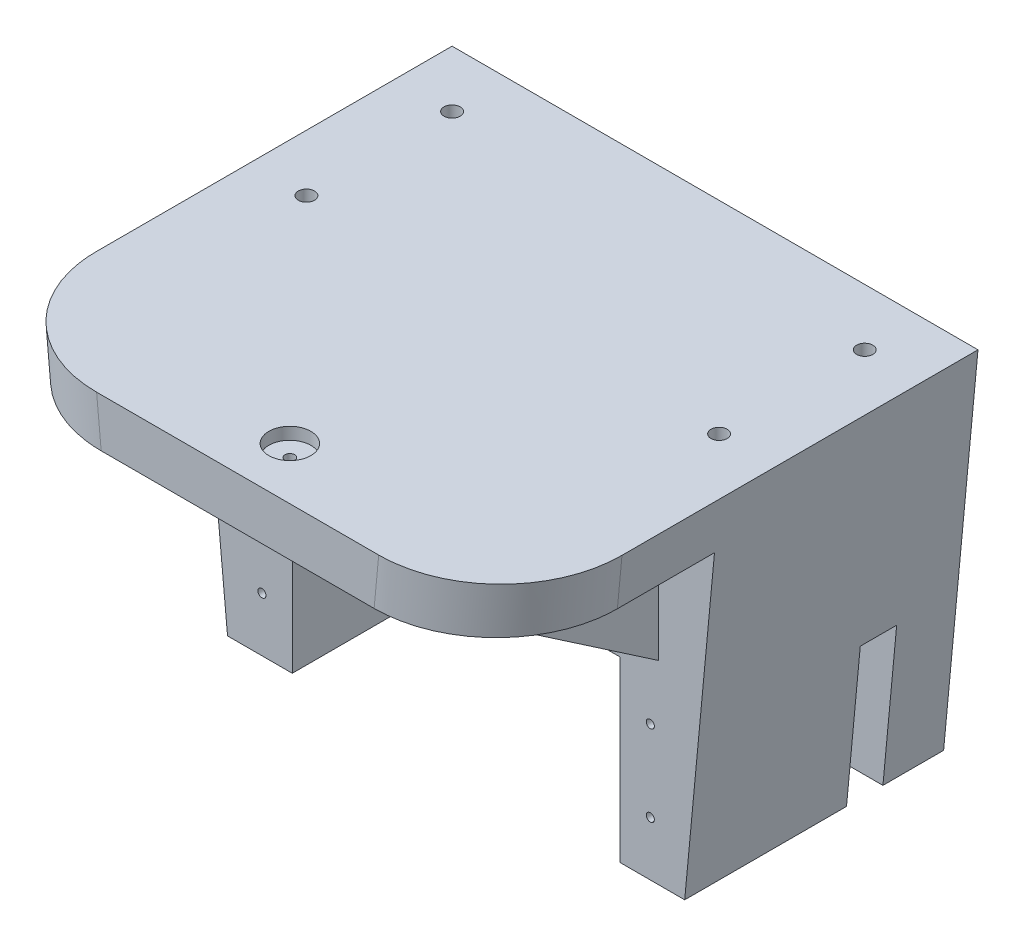
SolidWorks part; units mm, degrees
ref_plane "Plano frontal" through (0, 0, 0) normal (0, 0, 1) x (1, 0, 0)
ref_plane "Plano superior" through (0, 0, 0) normal (0, 1, 0) x (1, 0, 0)
ref_plane "Plano direito" through (0, 0, 0) normal (1, 0, 0) x (0, 0, -1)
sketch "Esboço1" plane through (0, 0, 0) normal (0, 0, 1) x (1, 0, 0)
  line L0 (-32.5, 31.3195) -> (32.5, 31.3195)
  line L1 (32.5, 31.3195) -> (28.25, -13.6805)
  line L2 (28.25, -13.6805) -> (20.25, -13.6805)
  line L3 (20.25, -13.6805) -> (20.25, 8.3195)
  line L4 (20.25, 8.3195) -> (-20.25, 8.3195)
  line L5 (-20.25, 8.3195) -> (-20.25, -13.6805)
  line L6 (-20.25, -13.6805) -> (-28.25, -13.6805)
  line L7 (-28.25, -13.6805) -> (-32.5, 31.3195)
  point P6 (0, 8.3195)
  point P9 (0, 31.3195)
  dimension "D1" = 40.5
  dimension "D2" = 22
  dimension "D3" = 8
  dimension "D4" = 8
  dimension "D5" = 65
  dimension "D6" = 22
  dimension "D7" = 45
extrude "Ressalto-extrusão1" add sketch "Esboço1" along normal blind 30
ref_plane "Plano1" through (40, 0, 0) normal (1, 0, 0) x (0, 0, -1)
sketch "Esboço3" plane through (40, 0, 0) normal (1, 0, 0) x (0, 0, -1)
  line L0 (-10, -13.6805) -> (-10, 4.3195)
  line L1 (-30, -13.6805) -> (0, -13.6805) construction
  line L2 (-10, 4.3195) -> (-5.5, 4.3195)
  line L3 (-5.5, 4.3195) -> (-5.5, -13.6805)
  line L4 (-30, -13.6805) -> (-30, 31.3195) construction
  line L5 (-10, -13.6805) -> (-5.5, -13.6805)
  dimension "D1" = 20
  dimension "D2" = 18
  dimension "D3" = 4.5
extrude "Corte-extrusão2" cut sketch "Esboço3" against normal blind 28.5
sketch "Esboço4" plane through (0, 0, 0) normal (0, 0, -1) x (-1, 0, 0)
  line L0 (-32.5, 31.3195) -> (32.5, 31.3195)
  line L1 (32.5, 31.3195) -> (28.25, -13.6805)
  line L2 (28.25, -13.6805) -> (20.25, -13.6805)
  line L6 (-20.25, -13.6805) -> (-28.25, -13.6805)
  line L7 (-28.25, -13.6805) -> (-32.5, 31.3195)
  line L8 (-20.25, -13.6805) -> (20.25, -13.6805)
extrude "Ressalto-extrusão2" add sketch "Esboço4" along normal blind 2
sketch "Esboço5" plane through (0, 0, 30) normal (0, 0, 1) x (1, 0, 0)
  line L0 (-24, 3.0195) -> (24, 3.0195) construction
  line L1 (-20.25, 8.3195) -> (20.25, 8.3195) construction
  circle A0 centre (-24, 3.0195) radius 0.5
  circle A1 centre (24, 3.0195) radius 0.5
  circle A2 centre (-24, -6.9805) radius 0.5
  circle A3 centre (24, -6.9805) radius 0.5
  point P6 (0, 8.3195)
  point P7 (0, 3.0195)
  dimension "D1" = 48
  dimension "D2" = 10
  dimension "D4" = 1
  dimension "D5" = 1
  dimension "D6" = 1
  dimension "D7" = 1
  dimension "D3" = 10
  dimension "D8" = 5.3
extrude "Corte-extrusão3" cut sketch "Esboço5" against normal blind 10
sketch "Esboço6" plane through (0, 31.3195, 0) normal (0, 1, 0) x (1, 0, 0)
  line L0 (-32.5, 2) -> (32.5, 2) construction
  line L1 (-32.5, -30) -> (-32.5, 2) construction
  line L2 (32.5, -30) -> (-32.5, -30) construction
  line L3 (32.5, -30) -> (32.5, 2) construction
  circle A0 centre (-25.5, -5) radius 1
  circle A1 centre (-25.5, -23) radius 1
  circle A2 centre (25.5, -5) radius 1
  circle A3 centre (25.5, -23) radius 1
  dimension "D1" = 7
  dimension "D3" = 2
  dimension "D6" = 2
  dimension "D11" = 2
  dimension "D12" = 2
  dimension "D2" = 7
  dimension "D4" = 7
  dimension "D5" = 7
  dimension "D7" = 7
  dimension "D8" = 7
  dimension "D9" = 7
  dimension "D10" = 7
extrude "Corte-extrusão4" cut sketch "Esboço6" against normal blind 10
sketch "Esboço7" plane through (0, 0, 30) normal (0, 0, 1) x (1, 0, 0)
  line L0 (-32.5, 31.3195) -> (32.5, 31.3195)
  line L1 (32.5, 31.3195) -> (31.9333, 25.3195)
  line L2 (28.25, -13.6805) -> (32.5, 31.3195) construction
  line L3 (31.9333, 25.3195) -> (-31.9333, 25.3195)
  line L4 (-32.5, 31.3195) -> (-28.25, -13.6805) construction
  line L5 (-31.9333, 25.3195) -> (-32.5, 31.3195)
  dimension "D1" = 6
extrude "Ressalto-extrusão3" add sketch "Esboço7" along normal blind 27
ref_plane "Plano3" through (20, 0, 0) normal (1, 0, 0) x (0, 0, -1)
sketch "Esboço10" plane through (20, 0, 0) normal (1, 0, 0) x (0, 0, -1)
  line L0 (-30, 25.3195) -> (-30, 10.3195)
  line L1 (-30, -13.6805) -> (-30, 25.3195) construction
  line L2 (-30, 10.3195) -> (-52, 25.3195)
  line L3 (-57, 25.3195) -> (-30, 25.3195) construction
  line L4 (-52, 25.3195) -> (-30, 25.3195)
  dimension "D1" = 22
  dimension "D2" = 15
extrude "Ressalto-extrusão4" add sketch "Esboço10" along normal blind 5
mirror "Espelhar1" about plane through (0, 0, 0) normal (1, 0, 0) of "Ressalto-extrusão4"
fillet "Filete1" radius 15 2 edges at (-32.2167, 28.3195, 57) (32.2167, 28.3195, 57)
sketch "Esboço11" plane through (0, 31.3195, 0) normal (0, 1, 0) x (1, 0, 0)
  line L0 (17.4333, -57) -> (-17.4333, -57) construction
  circle A0 centre (0, -50.55) radius 2.6
  dimension "D1" = 5.2
  dimension "D2" = 6.45
extrude "Corte-extrusão5" cut sketch "Esboço11" against normal blind 1.5
sketch "Esboço12" plane through (0, 29.8195, 0) normal (0, 1, 0) x (1, 0, 0)
  circle A0 centre (0, -50.55) radius 0.6
  dimension "D1" = 1.2
extrude "Corte-extrusão6" cut sketch "Esboço12" against normal up to vertex (4.5 mm away) up to point (16.8666, 25.3195, 57)
chamfer "Chanfro1" distance 0.5 angle 45 1 edges at (0, 25.3195, 51.15)
